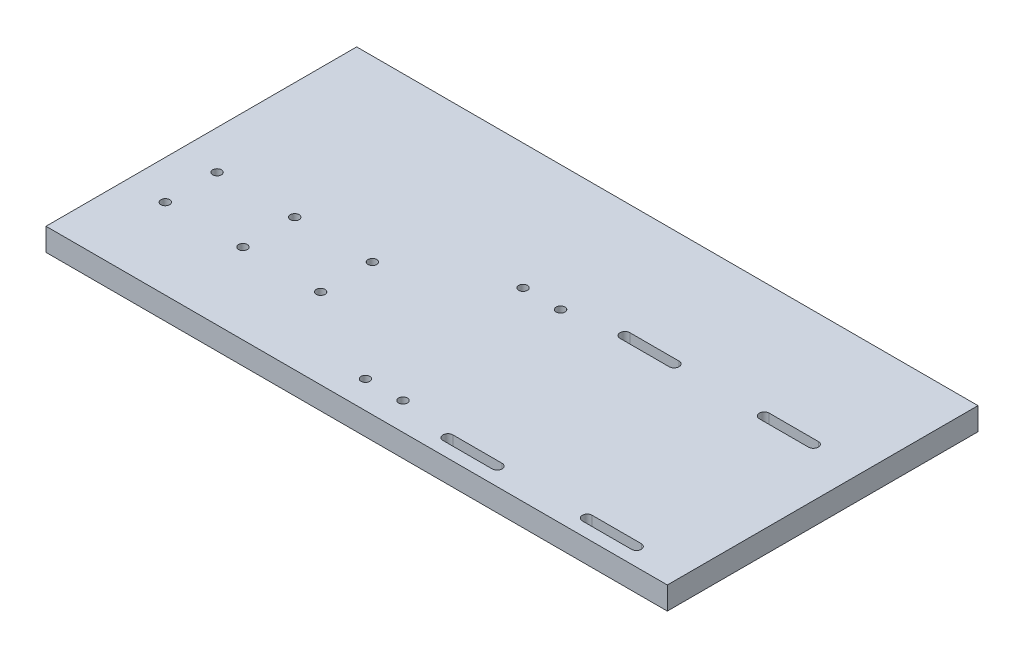
SolidWorks part; units mm, degrees
ref_plane "Front Plane" through (0, 0, 0) normal (0, 0, 1) x (1, 0, 0)
ref_plane "Top Plane" through (0, 0, 0) normal (0, 1, 0) x (1, 0, 0)
ref_plane "Right Plane" through (0, 0, 0) normal (1, 0, 0) x (0, 0, -1)
sketch "Sketch1" plane through (0, 0, 0) normal (0, 1, 0) x (1, 0, 0)
  line L1 (0, 0) -> (304.8, 0)
  line L2 (0, 0) -> (0, 152.4)
  line L3 (0, 152.4) -> (304.8, 152.4)
  line L4 (304.8, 0) -> (304.8, 152.4)
  dimension "D1" = 152.4
  dimension "D2" = 304.8
extrude "Boss-Extrude1" add sketch "Sketch1" along normal blind 11.1125
sketch "Sketch3" plane through (0, 11.1125, 0) normal (0, 1, 0) x (1, 0, 0)
  line L0 (200.4771, 52.1716) -> (268.8031, 52.1716) construction
  line L1 (200.4771, 8.763) -> (200.4771, 95.5802) construction
  line L2 (268.8031, 8.763) -> (268.8031, 95.5802) construction
  line L3 (256.7381, 8.763) -> (280.8681, 8.763)
  line L4 (256.7381, 11.176) -> (280.8681, 11.176)
  line L5 (280.8681, 6.35) -> (256.7381, 6.35)
  line L6 (256.7381, 95.5802) -> (280.8681, 95.5802)
  line L7 (256.7381, 93.1672) -> (280.8681, 93.1672)
  line L8 (280.8681, 97.9932) -> (256.7381, 97.9932)
  line L9 (234.6401, 8.763) -> (234.6401, 95.5802) construction
  line L10 (188.4121, 97.9932) -> (212.5421, 97.9932)
  line L11 (212.5421, 95.5802) -> (188.4121, 95.5802)
  line L12 (212.5421, 93.1672) -> (188.4121, 93.1672)
  line L13 (188.4121, 6.35) -> (212.5421, 6.35)
  line L14 (212.5421, 11.176) -> (188.4121, 11.176)
  line L15 (212.5421, 8.763) -> (188.4121, 8.763)
  line L16 (304.8, 0) -> (304.8, 152.4) construction
  line L17 (139.7, 13.5168) -> (165.1, 13.5168) construction
  line L18 (139.7, 97.1764) -> (165.1, 97.1764) construction
  line L19 (139.7, 97.1764) -> (139.7, 84.4764) construction
  line L20 (139.7, 84.4764) -> (165.1, 84.4764) construction
  line L21 (165.1, 97.1764) -> (165.1, 84.4764) construction
  line L22 (165.1, 19.8668) -> (139.7, 19.8668) construction
  line L23 (165.1, 19.8668) -> (165.1, 7.1668) construction
  line L24 (165.1, 7.1668) -> (139.7, 7.1668) construction
  line L25 (139.7, 19.8668) -> (139.7, 7.1668) construction
  line L26 (165.1, 90.8264) -> (139.7, 90.8264) construction
  line L27 (143.1925, 90.8264) -> (143.1925, 84.4764) construction
  line L28 (161.6075, 90.8264) -> (161.6075, 84.4764) construction
  line L29 (143.1925, 13.5168) -> (143.1925, 19.8668) construction
  line L30 (161.6075, 13.5168) -> (161.6075, 19.8668) construction
  line L31 (152.4, 90.8264) -> (152.4, 13.5168)
  line L32 (152.4, 52.1716) -> (200.4771, 52.1716)
  line L33 (0, 0) -> (304.8, 0) construction
  circle A0 centre (256.7381, 8.763) radius 2.413
  circle A1 centre (280.8681, 8.763) radius 2.413
  circle A2 centre (256.7381, 95.5802) radius 2.413
  circle A3 centre (280.8681, 95.5802) radius 2.413
  circle A4 centre (212.5421, 95.5802) radius 2.413
  circle A5 centre (188.4121, 95.5802) radius 2.413
  circle A6 centre (188.4121, 8.763) radius 2.413
  circle A7 centre (212.5421, 8.763) radius 2.413
  point P5 (200.4771, 52.1716)
  point P8 (268.8031, 52.1716)
  point P11 (268.8031, 8.763)
  point P28 (234.6401, 52.1716)
  dimension "D1" = 4.826
  dimension "D2" = 81.9912
  dimension "D3" = 44.196
  dimension "D4" = 24.13
  dimension "D5" = 35.9969
  dimension "D6" = 6.35
  dimension "D7" = 6.35
  dimension "D8" = 25.4
  dimension "D9" = 25.4
  dimension "D10" = 9.2075
  dimension "D11" = 9.2075
  dimension "D12" = 9.2075
  dimension "D13" = 9.2075
  dimension "D14" = 6.35
  dimension "D15" = 6.35
  dimension "D16" = 6.35
  dimension "D17" = 6.35
  dimension "D18" = 64.6096
  dimension "D19" = 6.35
  dimension "D20" = 152.4
extrude "Cut-Extrude1" cut sketch "Sketch3" against normal blind 11.1125
sketch "Sketch5" plane through (0, 0, -11.176) normal (0, 0, 1) x (1, 0, 0)
  line L0 (212.5421, 0) -> (212.5421, 11.1125) construction
  line L1 (188.4121, 0) -> (212.5421, 0)
  line L2 (188.4121, 0) -> (188.4121, 2.6778)
  line L3 (188.4121, 2.6778) -> (212.5421, 2.6778)
  line L4 (212.5421, 0) -> (212.5421, 2.6778)
  line L5 (280.8681, 0) -> (280.8681, 11.1125) construction
  line L6 (256.7381, 0) -> (280.8681, 0)
  line L7 (256.7381, 0) -> (256.7381, 2.54)
  line L8 (256.7381, 2.54) -> (280.8681, 2.54)
  line L9 (280.8681, 0) -> (280.8681, 2.54)
  dimension "D1" = 2.54
extrude "Cut-Extrude2" cut sketch "Sketch5" against normal up to next
sketch "Sketch7" plane through (0, 0, 0) normal (0, -1, 0) x (1, 0, 0)
  point P0 (161.6075, -13.5168)
  point P1 (143.1925, -13.5168)
  point P3 (143.1925, -90.8264)
  point P5 (161.6075, -90.8264)
hole_wizard "CBORE for #8 Socket Head Cap Screw1" positions "3DSketch5" profile "Sketch11" counterbore size "#8" standard "ANSI Inch" end condition up to next
sketch3d "3DSketch5"
  point P0 (161.6075, 0, -13.5168)
  point P3 (143.1925, 0, -13.5168)
  point P6 (161.6075, 0, -90.8264)
  point P9 (143.1925, 0, -90.8264)
sketch "Sketch11" plane through (161.6075, 0, -13.5168) normal (1, 0, 0) x (0, 0, -1)
  line L0 (0, 0) -> (0, 11.1125)
  line L1 (0, 11.1125) -> (2.1526, 11.1125)
  line L3 (2.1526, 11.1125) -> (2.1526, 4.1656)
  line L4 (2.1526, 4.1656) -> (3.9687, 4.1656)
  line L5 (3.9687, 4.1656) -> (3.9687, 0)
  line L7 (3.9687, 0) -> (0, 0)
  line L11 (0, -6.35) -> (0, 107.95) construction
  dimension "Thru Hole Dia." = 4.3053
  dimension "Thru Hole Depth" = 11.1125
  dimension "C'Bore Dia." = 7.9375
  dimension "C'Bore Depth" = 4.1656
sketch "Sketch18" plane through (0, 0, 0) normal (0, -1, 0) x (1, 0, 0)
  line L0 (152.4, -52.1716) -> (0, -52.1716)
  line L1 (0, -152.4) -> (0, 0) construction
  line L2 (95.25, -64.8716) -> (95.25, -39.4716)
  line L3 (57.15, -64.8716) -> (57.15, -39.4716)
  line L4 (19.05, -64.8716) -> (19.05, -39.4716)
  point P8 (95.25, -52.1716)
  point P10 (57.15, -52.1716)
  point P13 (19.05, -52.1716)
  point P14 (0, 0)
  dimension "D1" = 38.1
  dimension "D2" = 38.1
  dimension "D3" = 25.4
  dimension "D4" = 19.05
hole_wizard "CBORE for #8 Socket Head Cap Screw3" positions "3DSketch10" profile "Sketch19" counterbore size "#8" standard "ANSI Inch" end condition up to next
sketch3d "3DSketch10"
  point P0 (95.25, 0, -39.4716)
  point P3 (95.25, 0, -64.8716)
  point P6 (57.15, 0, -39.4716)
  point P9 (57.15, 0, -64.8716)
  point P12 (19.05, 0, -39.4716)
  point P15 (19.05, 0, -64.8716)
sketch "Sketch19" plane through (95.25, 0, -39.4716) normal (1, 0, 0) x (0, 0, -1)
  line L0 (0, 0) -> (0, 11.1125)
  line L1 (0, 11.1125) -> (2.1526, 11.1125)
  line L3 (2.1526, 11.1125) -> (2.1527, 4.1656)
  line L4 (2.1527, 4.1656) -> (3.9687, 4.1656)
  line L5 (3.9687, 4.1656) -> (3.9687, 0)
  line L7 (3.9687, 0) -> (0, 0)
  line L11 (0, -6.35) -> (0, 107.95) construction
  dimension "Thru Hole Dia." = 4.3053
  dimension "Thru Hole Depth" = 11.1125
  dimension "C'Bore Dia." = 7.9375
  dimension "C'Bore Depth" = 4.1656
